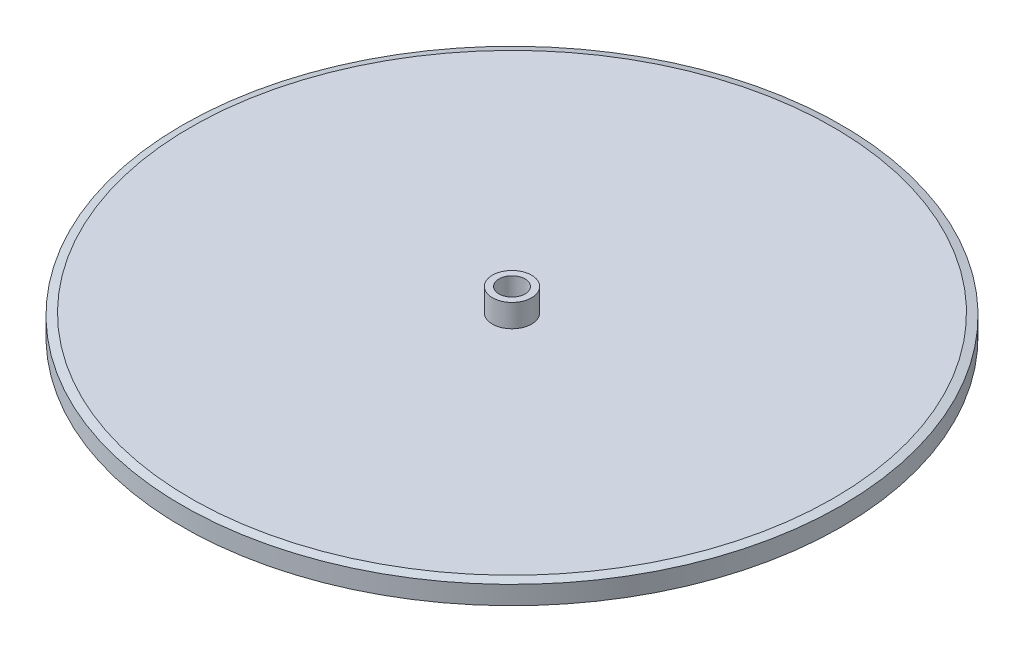
SolidWorks part; units mm, degrees
material "Сталь ШХ15 ГОСТ 801-78"
ref_plane "Plane1" through (0, 0, 0) normal (0, 0, 1) x (1, 0, 0)
ref_plane "Plane2" through (0, 0, 0) normal (0, 1, 0) x (1, 0, 0)
ref_plane "Plane3" through (0, 0, 0) normal (1, 0, 0) x (0, 0, -1)
sketch "Эскиз1" plane through (0, 0, 0) normal (0, 0, 1) x (1, 0, 0)
  line L0 (0, 0) -> (50.5, 0)
  line L1 (50.5, 0) -> (50.5, 3.5)
  line L2 (50.5, 3.5) -> (3, 3.5)
  line L3 (3, 3.5) -> (3, 7)
  line L4 (3, 7) -> (0, 7)
  line L5 (0, 7) -> (0, 0)
  dimension "D1" = 3.5
  dimension "30" = 50.5
  dimension "D3" = 3
  dimension "D4" = 3.5
ref_axis "Ось1" through (0, 7, 0) along (0, -1, 0)
revolve "Повернуть2" add sketch "Эскиз1" angle 360 about axis through (0, 7, 0) along (0, -1, 0)
chamfer "Фаска1" distance 1.25 angle 15 1 edges at (-50.5, 3.5, 0)
chamfer "Фаска2" distance 1.25 angle 15 1 edges at (-50.5, 0, 0)
sketch "Эскиз2" plane through (0, 0, 0) normal (0, -1, 0) x (-1, 0, 0)
  circle A0 centre (0, 0) radius 2
  dimension "D1" = 4
sketch "Эскиз3" plane through (0, 0, 0) normal (0, 0, 1) x (1, 0, 0)
  circle A0 centre (0, 5.828) radius 1
extrude "Вырез-Вытянуть3" cut sketch "Эскиз2" against normal through all both contours A0
